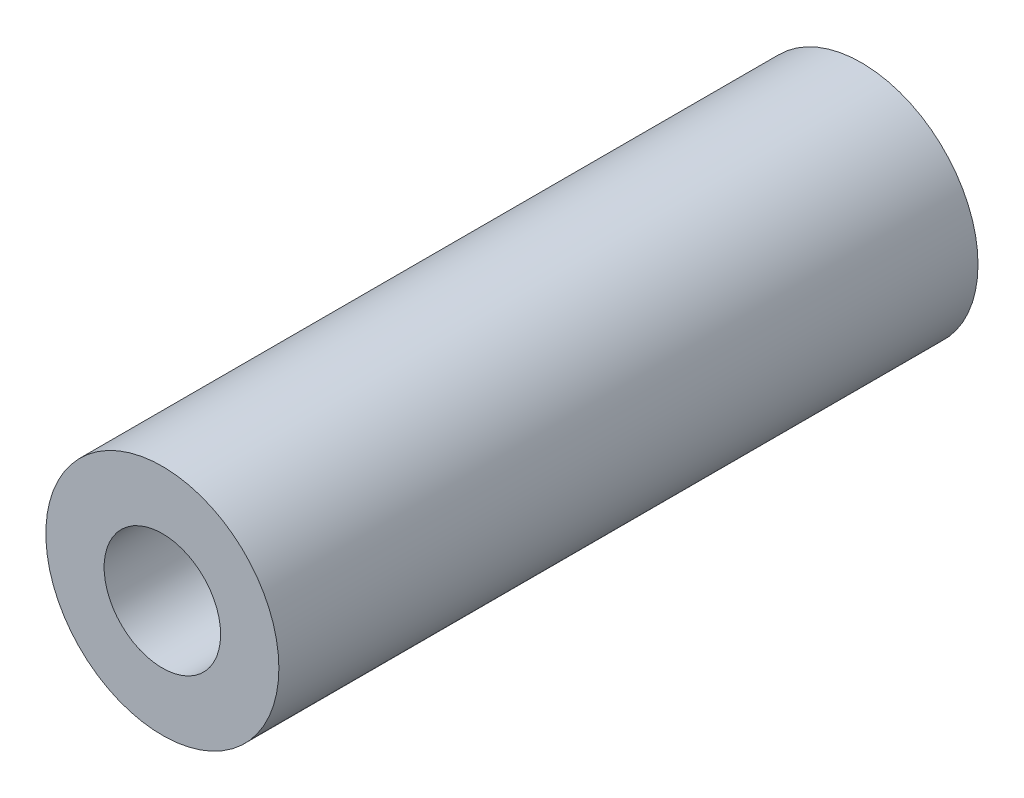
SolidWorks part; units mm, degrees
ref_plane "Front Plane" through (0, 0, 0) normal (0, 0, 1) x (1, 0, 0)
ref_plane "Top Plane" through (0, 0, 0) normal (0, 1, 0) x (1, 0, 0)
ref_plane "Right Plane" through (0, 0, 0) normal (1, 0, 0) x (0, 0, -1)
sketch "Sketch1" plane through (0, 0, 0) normal (0, 0, 1) x (1, 0, 0)
  circle A0 centre (0, 0) radius 5
  circle A1 centre (0, 0) radius 2.5
  dimension "D1" = 10
  dimension "D2" = 5
extrude "Boss-Extrude1" add sketch "Sketch1" along normal blind 30
